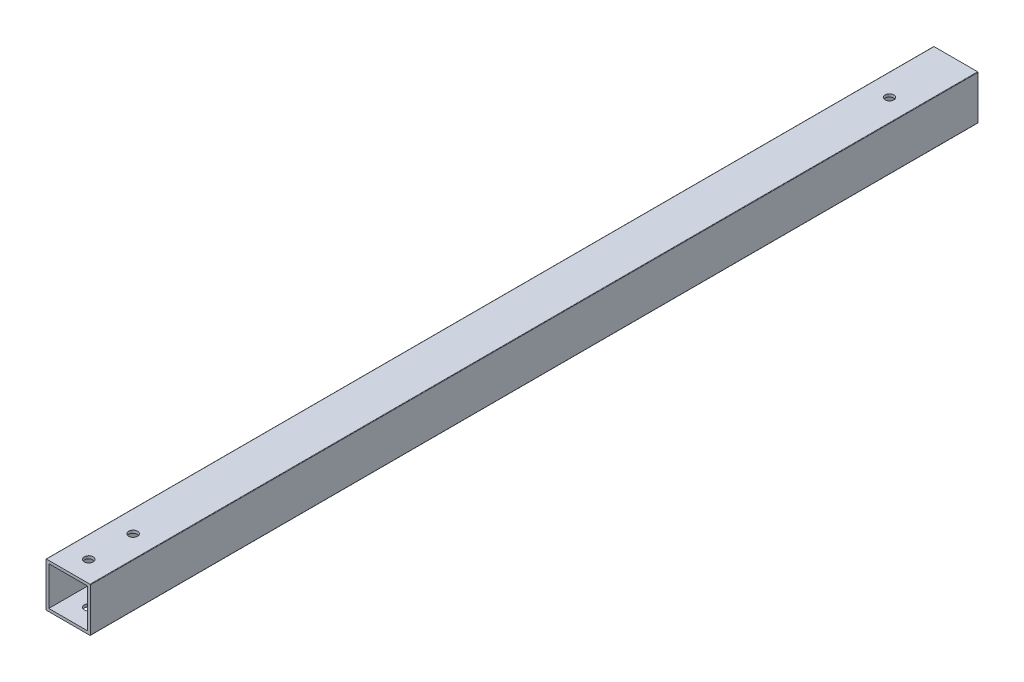
SolidWorks part; units mm, degrees
material "1060 Alloy"
ref_plane "Front Plane" through (0, 0, 0) normal (0, 0, 1) x (1, 0, 0)
ref_plane "Top Plane" through (0, 0, 0) normal (0, 1, 0) x (1, 0, 0)
ref_plane "Right Plane" through (0, 0, 0) normal (1, 0, 0) x (0, 0, -1)
ref_plane "Plane1" through (0, 0, 0) normal (0, 0, -1) x (-1, 0, 0)
sketch "Sketch1" plane through (0, 0, 0) normal (0, 0, -1) x (-1, 0, 0)
  line L4 (1.5875, -1.3335) -> (1.5875, 23.5585)
  line L5 (1.3335, 23.8125) -> (-23.5585, 23.8125)
  line L6 (-23.8125, 23.5585) -> (-23.8125, -1.3335)
  line L7 (-23.5585, -1.5875) -> (1.3335, -1.5875)
  line L9 (0, 22.225) -> (-22.225, 22.225)
  line L10 (0, 22.225) -> (0, 0)
  line L11 (0, 0) -> (-22.225, 0)
  line L12 (-22.225, 22.225) -> (-22.225, 0)
  line L13 (0, 22.225) -> (-22.225, 0) construction
  line L14 (0, 0) -> (-22.225, 22.225) construction
  arc A4 (1.3335, -1.5875) -> (1.5875, -1.3335) centre (1.3335, -1.3335) ccw
  arc A5 (1.5875, 23.5585) -> (1.3335, 23.8125) centre (1.3335, 23.5585) ccw
  arc A6 (-23.5585, 23.8125) -> (-23.8125, 23.5585) centre (-23.5585, 23.5585) ccw
  arc A7 (-23.8125, -1.3335) -> (-23.5585, -1.5875) centre (-23.5585, -1.3335) ccw
  point P24 (-11.1125, 11.1125)
  dimension "D1" = 25.4
  dimension "D2" = 25.4
  dimension "D3" = 1.5875
  dimension "D4" = 1.5875
  dimension "D5" = 1.5875
extrude "Boss-Extrude1" add sketch "Sketch1" against normal blind 508
sketch "Sketch2" plane through (-1.5875, 0, 0) normal (-1, 0, 0) x (0, 0, 1)
  line L0 (0, -1.3335) -> (0, 23.5585) construction
  line L1 (508, -1.3335) -> (0, -1.3335) construction
  line L2 (508, -1.3335) -> (508, 23.5585) construction
  circle A0 centre (12.6975, 11.3665) radius 1.5875
  circle A1 centre (495.3, 11.3665) radius 1.5875
  circle A2 centre (76.2, 11.3665) radius 6.35
  circle A3 centre (431.8, 11.3665) radius 6.35
  point P4 (0, 11.1125)
  dimension "D1" = 3.175
  dimension "D2" = 12.7
  dimension "D3" = 12.7
  dimension "D4" = 3.175
  dimension "D5" = 12.7
  dimension "D6" = 12.7
  dimension "D7" = 12.7
  dimension "D8" = 12.7
  dimension "D9" = 76.2
  dimension "D10" = 12.7
  dimension "D11" = 12.7
  dimension "D12" = 76.2
extrude "Cut-Extrude1" [suppressed] cut sketch "Sketch2" against normal through all
sketch "Sketch4" plane through (23.8125, 0, 0) normal (1, 0, 0) x (0, 0, -1)
  line L2 (-40.3145, 9.8425) -> (-40.3145, 12.3825)
  line L4 (-35.552, 9.8425) -> (-35.552, 12.3825)
  line L6 (-40.3145, 12.3825) -> (-35.552, 12.3825)
  line L7 (-40.3145, 11.1125) -> (-35.552, 11.1125)
  line L8 (0, 23.5585) -> (0, -1.3335) construction
  line L9 (0, 11.1125) -> (-49.6378, 11.1125)
  circle A0 centre (-37.9333, 9.8425) radius 2.3812
  circle A1 centre (-37.9333, 12.3825) radius 2.3812
  dimension "D1" = 4.7625
  dimension "D2" = 37.9333
  dimension "D3" = 1.27
extrude "Cut-Extrude2" [suppressed] cut sketch "Sketch4" against normal through all contours L6 A1 | L6 A1 A0 | L9 A0 | L9 A1 | A1 A0 | A0 L4 L7 | A1 L7 L4 | A0 L7 L2 | A1 L2 L7
sketch "Sketch7" plane through (0, -1.5875, 0) normal (0, -1, 0) x (1, 0, 0)
  circle A0 centre (10.9125, 470.65) radius 2.54
  circle A1 centre (10.9125, 496.05) radius 2.54
extrude "Cut-Extrude5" cut sketch "Sketch7" against normal through all
sketch "Sketch8" plane through (0, 23.8125, 0) normal (0, 1, 0) x (1, 0, 0)
  line L0 (11.1125, 0) -> (11.1125, -37.9333) construction
  line L1 (-1.3335, 0) -> (23.5585, 0) construction
  circle A0 centre (11.1125, -37.9333) radius 2.4892
  dimension "D2" = 4.9784
  dimension "D1" = 37.9333
extrude "Cut-Extrude6" cut sketch "Sketch8" against normal blind 25.4
